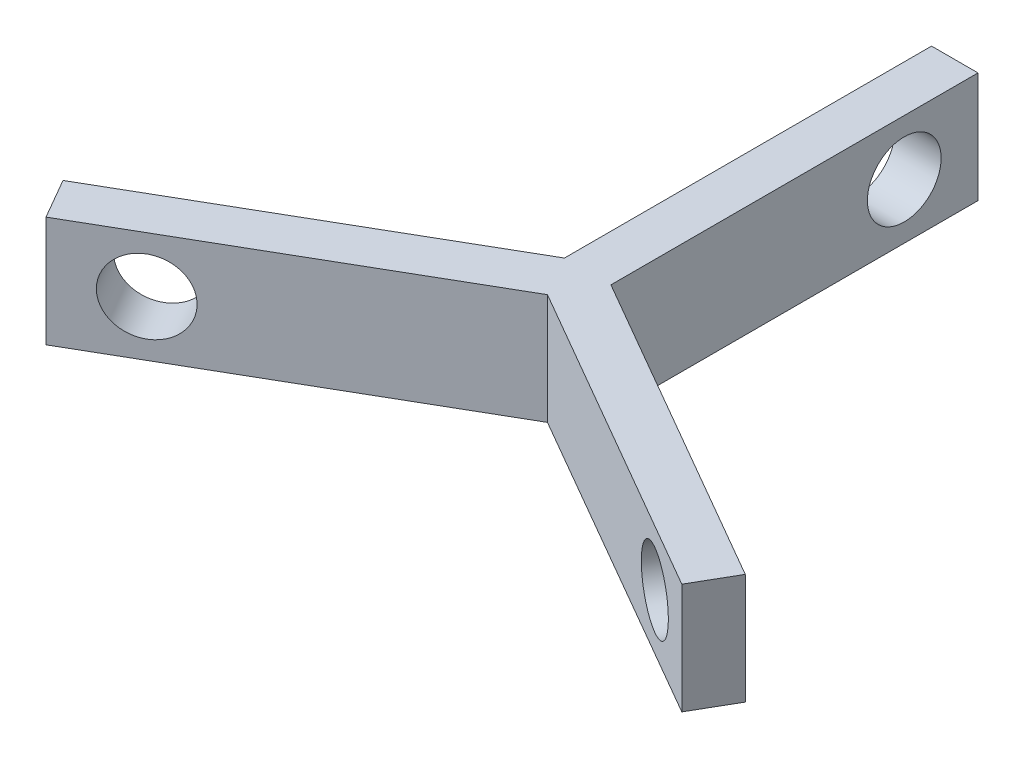
SolidWorks part; units mm, degrees
material "Balsa"
ref_plane "Alzado" through (0, 0, 0) normal (0, 0, 1) x (1, 0, 0)
ref_plane "Planta" through (0, 0, 0) normal (0, 1, 0) x (1, 0, 0)
ref_plane "Vista lateral" through (0, 0, 0) normal (1, 0, 0) x (0, 0, -1)
sketch "Croquis1" plane through (0, 0, 0) normal (0, 1, 0) x (1, 0, 0)
  line L9 (0, 40.9535) -> (0, 0) construction
  line L10 (0, 0) -> (-35.4668, -20.4767) construction
  line L11 (0, 0) -> (35.4668, -20.4767) construction
  line L12 (-2.5, 40.9535) -> (2.5, 40.9535)
  line L13 (34.2168, -22.6418) -> (36.7168, -18.3117)
  line L14 (-36.7168, -18.3117) -> (-34.2168, -22.6418)
  line L15 (2.5, 40.9535) -> (2.5, 1.4434)
  line L16 (2.5, 1.4434) -> (36.7168, -18.3117)
  line L17 (-2.5, 40.9535) -> (-2.5, 1.4434)
  line L18 (-2.5, 1.4434) -> (-36.7168, -18.3117)
  line L19 (-34.2168, -22.6418) -> (0, -2.8868)
  line L20 (0, -2.8868) -> (34.2168, -22.6418)
  point P2 (0, 38.969)
  point P7 (0, 40.9535)
  point P10 (35.4668, -20.4767)
  point P14 (-35.4668, -20.4767)
  point P18 (0, 35)
  dimension "D1" = 120
  dimension "D2" = 5
  dimension "D4" = 120
  dimension "D3" = 3.969
  dimension "D5" = 1.9845
  dimension "D6" = 35
extrude "Saliente-Extruir1" add sketch "Croquis1" along normal mid plane 11.907
sketch "Croquis2" plane through (-1.25, 0, 2.1651) normal (-0.5, 0, 0.866) x (0.866, 0, 0.5)
  line L0 (40.9535, 5.9535) -> (40.9535, -5.9535) construction
  circle A0 centre (33.0155, 0) radius 3.969
  dimension "D1" = 7.938
  dimension "D2" = 7.938
extrude "Cortar-Extruir1" cut sketch "Croquis2" against normal up to next (5 mm away)
pattern_circular "MatrizC1" count 3 every 120 about axis through (0, 5.9535, 0) along (0, 1, 0) of "Cortar-Extruir1"
equation "\"L\"=40"
equation "\"r\"= 3.969"
equation "\"D3@Croquis1\"=\"r\""
equation "\"D5@Croquis1\"=\"r\"*0.5"
equation "\"d\"= 35"
equation "\"D6@Croquis1\"=\"d\""
equation "\"D1@Croquis2\"=\"r\"*2"
equation "\"D2@Croquis2\"=\"r\"*2"
equation "\"D1@Saliente-Extruir1\"=\"r\"*3"
